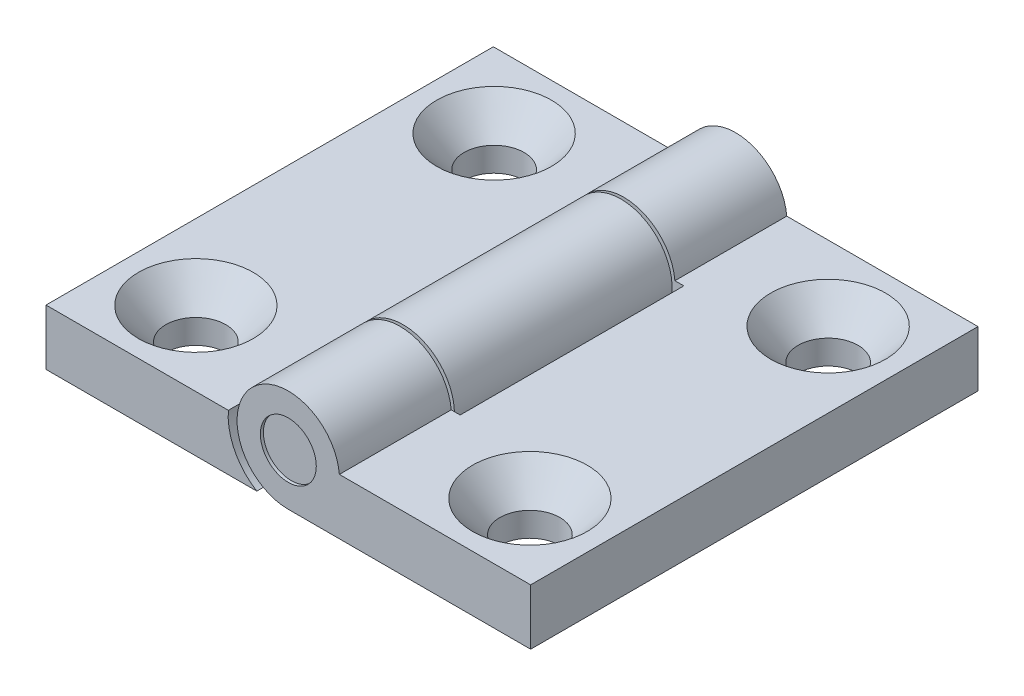
SolidWorks part; units mm, degrees
ref_plane "Front" through (0, 0, 0) normal (0, 0, 1) x (1, 0, 0)
ref_plane "Top" through (0, 0, 0) normal (0, 1, 0) x (1, 0, 0)
ref_plane "Right" through (0, 0, 0) normal (1, 0, 0) x (0, 0, -1)
sketch "Sketch1" plane through (0, 0, 0) normal (0, 0, 1) x (1, 0, 0)
  line L0 (4.3487, 4.7498) -> (20.6375, 4.7498)
  line L1 (-20.6375, 0) -> (20.6375, 0)
  line L2 (-20.6375, 0) -> (-20.6375, 4.7498)
  line L3 (-20.6375, 4.7498) -> (-4.3487, 4.7498)
  line L4 (20.6375, 0) -> (20.6375, 4.7498)
  circle A0 centre (0, 4.3656) radius 2.3813
  arc A1 (4.3487, 4.7498) -> (-4.3487, 4.7498) centre (0, 4.3656) ccw
  point P7 (0, 0)
  dimension "D1" = 8.7312
  dimension "D3" = 4.7625
  dimension "D2" = 4.7498
  dimension "D4" = 41.275
extrude "Extrude1" add sketch "Sketch1" along normal mid plane 38.1
sketch "Sketch2" plane through (0, 0, 19.05) normal (0, 0, 1) x (1, 0, 0)
  line L0 (-5.1107, 4.7498) -> (-4.3487, 4.7498)
  line L1 (0, 0) -> (-2.6848, 0)
  arc A0 (-4.3487, 4.7498) -> (0, 0) centre (0, 4.3656) ccw
  arc A1 (4.3487, 4.7498) -> (-4.3487, 4.7498) centre (0, 4.3656) ccw construction
  arc A2 (-5.1107, 4.7498) -> (-2.6848, 0) centre (0, 4.3656) ccw
  dimension "D1" = 0.762
extrude "Cut-Extrude1" cut sketch "Sketch2" against normal blind 9.525
mirror "Mirror1" about plane through (0, 0, 0) normal (0, 0, 1) of "Cut-Extrude1"
sketch "Sketch3" plane through (0, 0, 0) normal (0, 0, 1) x (1, 0, 0)
  line L0 (0, 9.8705) -> (0, -1.2724) construction
  line L1 (4.3487, 4.7498) -> (5.1107, 4.7498)
  line L2 (-2.6848, 0) -> (0, 0)
  line L3 (-4.3487, 4.7498) -> (-5.1107, 4.7498)
  line L4 (0, 0) -> (2.6848, 0)
  arc A0 (5.1107, 4.7498) -> (2.6848, 0) centre (0, 4.3656) cw
  arc A2 (-5.1107, 4.7498) -> (-2.6848, 0) centre (0, 4.3656) ccw
  arc A3 (-4.3487, 4.7498) -> (0, 0) centre (0, 4.3656) ccw
  arc A5 (0, 0) -> (4.3487, 4.7498) centre (0, 4.3656) ccw
  dimension "D1" = 0
extrude "Cut-Extrude2" cut sketch "Sketch3" against normal mid plane 19.05
sketch "Sketch4" plane through (0, 0, 0) normal (0, 1, 0) x (1, 0, 0)
  line L0 (-5.1107, 9.525) -> (-5.1107, 9.271)
  line L1 (5.1107, 9.525) -> (-5.1107, 9.525)
  line L2 (5.1107, 9.525) -> (5.1107, 9.271)
  line L3 (5.1107, 9.271) -> (-5.1107, 9.271)
  line L4 (-5.1107, 9.525) -> (-5.1107, 19.05) construction
  line L5 (-5.1107, -9.271) -> (5.1107, -9.271)
  line L6 (-5.1107, -9.271) -> (-5.1107, -9.525)
  line L7 (-5.1107, -9.525) -> (5.1107, -9.525)
  line L8 (5.1107, -9.271) -> (5.1107, -9.525)
  line L9 (-5.1107, -9.525) -> (-5.1107, -19.05) construction
  dimension "D1" = 0.254
  dimension "D2" = 0.254
extrude "Cut-Extrude4" cut sketch "Sketch4" along normal through all
sketch "Sketch5" plane through (0, 0, 0) normal (0, 0, 1) x (1, 0, 0)
  circle A0 centre (0, 4.3656) radius 2.3813
  dimension "D1" = 4.7625
extrude "Extrude2" add sketch "Sketch5" along normal mid plane 37.592
hole_wizard "CSK for #10 Flat Head Machine Screw1" positions "Sketch7" profile "Sketch6" countersink size "#10" standard "Ansi Inch" end condition through all
sketch "Sketch7" plane through (0, 4.7498, 0) normal (0, 1, 0) x (-1, 0, 0)
  line L0 (0, 20.2095) -> (0, -21.445) construction
  line L1 (-8.9184, 0) -> (9.9085, 0) construction
  point P0 (14.224, -12.7)
  point P1 (14.224, 12.7)
  point P2 (-14.224, 12.7)
  point P3 (-14.224, -12.7)
  dimension "D1" = 28.448
  dimension "D2" = 25.4
sketch "Sketch6" plane through (-14.224, 4.7498, -12.7) normal (1, 0, 0) x (0, 0, 1)
  line L0 (0, 0) -> (0, 4.7498)
  line L1 (0, 4.7498) -> (2.5527, 4.7498)
  line L2 (2.5527, 4.7498) -> (2.5527, 2.6882)
  line L3 (2.5527, 2.6882) -> (4.8895, 0)
  line L5 (4.8895, 0) -> (0, 0)
  line L6 (-2.5527, 2.6882) -> (-4.8895, 0) construction
  line L11 (0, -6.35) -> (0, 107.95) construction
  dimension "Thru Hole Dia." = 5.1054
  dimension "Thru Hole Depth" = 4.7498
  dimension "Near C'Sink Dia." = 9.779
  dimension "Near C'Sink Angle" = 82
